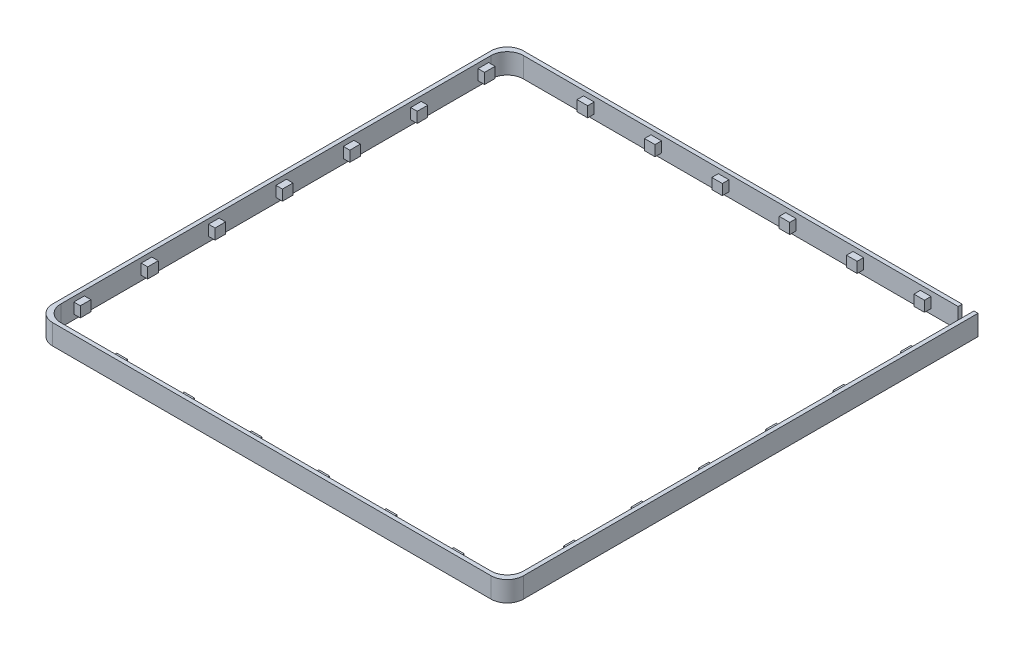
SolidWorks part; units mm, degrees
ref_plane "前视基准面" through (0, 0, 0) normal (0, 0, 1) x (1, 0, 0)
ref_plane "上视基准面" through (0, 0, 0) normal (0, 1, 0) x (1, 0, 0)
ref_plane "右视基准面" through (0, 0, 0) normal (1, 0, 0) x (0, 0, -1)
sketch "草图1" plane through (0, 0, 0) normal (0, 1, 0) x (1, 0, 0)
  line L1 (-29, 29) -> (29, 29)
  line L2 (-29, 29) -> (-29, -29)
  line L3 (-29, -29) -> (29, -29)
  line L4 (29, 29) -> (29, -29)
  line L5 (-29, 29) -> (29, -29) construction
  line L6 (-29, -29) -> (29, 29) construction
  point P0 (0, 0)
extrude "凸台-拉伸1" add sketch "草图1" along normal blind 2.5
sketch "草图2" plane through (0, 2.5, 0) normal (0, 1, 0) x (1, 0, 0)
  line L1 (-28.5, 28.5) -> (28.5, 28.5)
  line L2 (-28.5, 28.5) -> (-28.5, -28.5)
  line L3 (-28.5, -28.5) -> (28.5, -28.5)
  line L4 (28.5, 28.5) -> (28.5, -28.5)
  line L5 (-28.5, 28.5) -> (28.5, -28.5) construction
  line L6 (-28.5, -28.5) -> (28.5, 28.5) construction
  point P0 (0, 0)
extrude "切除-拉伸7" cut sketch "草图2" against normal through all and the other way through all
sketch "草图5" plane through (0, 0, -28.5) normal (0, 0, 1) x (1, 0, 0)
  line L0 (28.5, 2.5) -> (-28.5, 2.5) construction
  line L1 (28.5, 0) -> (27.0573, 0)
  line L2 (28.5, 0) -> (28.5, 2.5)
  line L3 (28.5, 2.5) -> (27.0573, 2.5)
  line L4 (27.0573, 0) -> (27.0573, 2.5)
extrude "切除-拉伸8" cut sketch "草图5" against normal through all
sketch "草图6" plane through (0, 0, -28.5) normal (0, 0, 1) x (1, 0, 0)
  line L0 (14.1073, 1.9) -> (14.1073, 0.6)
  line L5 (22.4073, 1.9) -> (23.7073, 1.9)
  line L6 (22.4073, 1.9) -> (22.4073, 0.6)
  line L7 (22.4073, 0.6) -> (23.7073, 0.6)
  line L8 (23.7073, 1.9) -> (23.7073, 0.6)
  line L9 (22.4073, 1.9) -> (23.7073, 0.6) construction
  line L10 (22.4073, 0.6) -> (23.7073, 1.9) construction
  line L11 (14.1073, 1.9) -> (15.4073, 1.9)
  line L12 (15.4073, 1.9) -> (15.4073, 0.6)
  line L13 (14.1073, 0.6) -> (15.4073, 0.6)
  line L14 (5.8073, 1.9) -> (5.8073, 0.6)
  line L15 (5.8073, 1.9) -> (7.1073, 1.9)
  line L16 (7.1073, 1.9) -> (7.1073, 0.6)
  line L17 (5.8073, 0.6) -> (7.1073, 0.6)
  line L18 (-2.4927, 1.9) -> (-2.4927, 0.6)
  line L19 (-2.4927, 1.9) -> (-1.1927, 1.9)
  line L20 (-1.1927, 1.9) -> (-1.1927, 0.6)
  line L21 (-2.4927, 0.6) -> (-1.1927, 0.6)
  line L22 (-10.7927, 1.9) -> (-10.7927, 0.6)
  line L23 (-10.7927, 1.9) -> (-9.4927, 1.9)
  line L24 (-9.4927, 1.9) -> (-9.4927, 0.6)
  line L25 (-10.7927, 0.6) -> (-9.4927, 0.6)
  line L26 (-19.0927, 1.9) -> (-19.0927, 0.6)
  line L27 (-19.0927, 1.9) -> (-17.7927, 1.9)
  line L28 (-17.7927, 1.9) -> (-17.7927, 0.6)
  line L29 (-19.0927, 0.6) -> (-17.7927, 0.6)
  line L34 (-27.3927, 1.9) -> (-27.3927, 0.6) [skipped]
  line L35 (-27.3927, 0.6) -> (-26.0927, 0.6) [skipped]
  line L36 (-26.0927, 1.9) -> (-26.0927, 0.6) [skipped]
  line L37 (-27.3927, 1.9) -> (-26.0927, 1.9) [skipped]
  dimension "D1" = 7
extrude "凸台-拉伸5" add sketch "草图6" along normal blind 0.8
fillet "圆角4" radius 2 3 edges at (28.5, 1.25, 28.5) (-28.5, 1.25, 28.5) (-28.5, 1.25, -28.5)
fillet "圆角5" radius 2 3 edges at (29, 1.25, 29) (-29, 1.25, 29) (-29, 1.25, -29)
sketch "草图8" plane through (-28.5, 0, 0) normal (1, 0, 0) x (0, 0, -1)
  line L0 (16.6073, 1.9) -> (16.6073, 0.6)
  line L5 (24.9073, 1.9) -> (26.2073, 1.9)
  line L6 (24.9073, 1.9) -> (24.9073, 0.6)
  line L7 (24.9073, 0.6) -> (26.2073, 0.6)
  line L8 (26.2073, 1.9) -> (26.2073, 0.6)
  line L9 (24.9073, 1.9) -> (26.2073, 0.6) construction
  line L10 (24.9073, 0.6) -> (26.2073, 1.9) construction
  line L11 (16.6073, 1.9) -> (17.9073, 1.9)
  line L12 (17.9073, 1.9) -> (17.9073, 0.6)
  line L13 (16.6073, 0.6) -> (17.9073, 0.6)
  line L14 (8.3073, 1.9) -> (8.3073, 0.6)
  line L15 (8.3073, 1.9) -> (9.6073, 1.9)
  line L16 (9.6073, 1.9) -> (9.6073, 0.6)
  line L17 (8.3073, 0.6) -> (9.6073, 0.6)
  line L18 (0.0073, 1.9) -> (0.0073, 0.6)
  line L19 (0.0073, 1.9) -> (1.3073, 1.9)
  line L20 (1.3073, 1.9) -> (1.3073, 0.6)
  line L21 (0.0073, 0.6) -> (1.3073, 0.6)
  line L22 (-8.2927, 1.9) -> (-8.2927, 0.6)
  line L23 (-8.2927, 1.9) -> (-6.9927, 1.9)
  line L24 (-6.9927, 1.9) -> (-6.9927, 0.6)
  line L25 (-8.2927, 0.6) -> (-6.9927, 0.6)
  line L26 (-16.5927, 1.9) -> (-16.5927, 0.6)
  line L27 (-16.5927, 1.9) -> (-15.2927, 1.9)
  line L28 (-15.2927, 1.9) -> (-15.2927, 0.6)
  line L29 (-16.5927, 0.6) -> (-15.2927, 0.6)
  line L30 (-24.8927, 1.9) -> (-24.8927, 0.6)
  line L31 (-24.8927, 1.9) -> (-23.5927, 1.9)
  line L32 (-23.5927, 1.9) -> (-23.5927, 0.6)
  line L33 (-24.8927, 0.6) -> (-23.5927, 0.6)
  dimension "D1" = 7
extrude "凸台-拉伸6" add sketch "草图8" along normal blind 0.8
sketch "草图10" plane through (0, 0, 28.5) normal (0, 0, -1) x (-1, 0, 0)
  line L0 (19.1073, 1.9) -> (19.1073, 0.6)
  line L11 (19.1073, 1.9) -> (20.4073, 1.9)
  line L12 (20.4073, 1.9) -> (20.4073, 0.6)
  line L13 (19.1073, 0.6) -> (20.4073, 0.6)
  line L14 (10.8073, 1.9) -> (10.8073, 0.6)
  line L15 (10.8073, 1.9) -> (12.1073, 1.9)
  line L16 (12.1073, 1.9) -> (12.1073, 0.6)
  line L17 (10.8073, 0.6) -> (12.1073, 0.6)
  line L18 (2.5073, 1.9) -> (2.5073, 0.6)
  line L19 (2.5073, 1.9) -> (3.8073, 1.9)
  line L20 (3.8073, 1.9) -> (3.8073, 0.6)
  line L21 (2.5073, 0.6) -> (3.8073, 0.6)
  line L22 (-5.7927, 1.9) -> (-5.7927, 0.6)
  line L23 (-5.7927, 1.9) -> (-4.4927, 1.9)
  line L24 (-4.4927, 1.9) -> (-4.4927, 0.6)
  line L25 (-5.7927, 0.6) -> (-4.4927, 0.6)
  line L26 (-14.0927, 1.9) -> (-14.0927, 0.6)
  line L27 (-14.0927, 1.9) -> (-12.7927, 1.9)
  line L28 (-12.7927, 1.9) -> (-12.7927, 0.6)
  line L29 (-14.0927, 0.6) -> (-12.7927, 0.6)
  line L30 (-22.3927, 1.9) -> (-22.3927, 0.6)
  line L31 (-22.3927, 1.9) -> (-21.0927, 1.9)
  line L32 (-21.0927, 1.9) -> (-21.0927, 0.6)
  line L33 (-22.3927, 0.6) -> (-21.0927, 0.6)
extrude "凸台-拉伸8" add sketch "草图10" along normal blind 0.8
sketch "草图12" plane through (28.5, 0, 0) normal (-1, 0, 0) x (0, 0, 1)
  line L0 (19.4573, 1.9) -> (19.4573, 0.6)
  line L11 (19.4573, 1.9) -> (20.7573, 1.9)
  line L12 (20.7573, 1.9) -> (20.7573, 0.6)
  line L13 (19.4573, 0.6) -> (20.7573, 0.6)
  line L14 (11.1573, 1.9) -> (11.1573, 0.6)
  line L15 (11.1573, 1.9) -> (12.4573, 1.9)
  line L16 (12.4573, 1.9) -> (12.4573, 0.6)
  line L17 (11.1573, 0.6) -> (12.4573, 0.6)
  line L18 (2.8573, 1.9) -> (2.8573, 0.6)
  line L19 (2.8573, 1.9) -> (4.1573, 1.9)
  line L20 (4.1573, 1.9) -> (4.1573, 0.6)
  line L21 (2.8573, 0.6) -> (4.1573, 0.6)
  line L22 (-5.4427, 1.9) -> (-5.4427, 0.6)
  line L23 (-5.4427, 1.9) -> (-4.1427, 1.9)
  line L24 (-4.1427, 1.9) -> (-4.1427, 0.6)
  line L25 (-5.4427, 0.6) -> (-4.1427, 0.6)
  line L26 (-13.7427, 1.9) -> (-13.7427, 0.6)
  line L27 (-13.7427, 1.9) -> (-12.4427, 1.9)
  line L28 (-12.4427, 1.9) -> (-12.4427, 0.6)
  line L29 (-13.7427, 0.6) -> (-12.4427, 0.6)
  line L30 (-22.0427, 1.9) -> (-22.0427, 0.6)
  line L31 (-22.0427, 1.9) -> (-20.7427, 1.9)
  line L32 (-20.7427, 1.9) -> (-20.7427, 0.6)
  line L33 (-22.0427, 0.6) -> (-20.7427, 0.6)
extrude "凸台-拉伸9" add sketch "草图12" along normal blind 0.8
